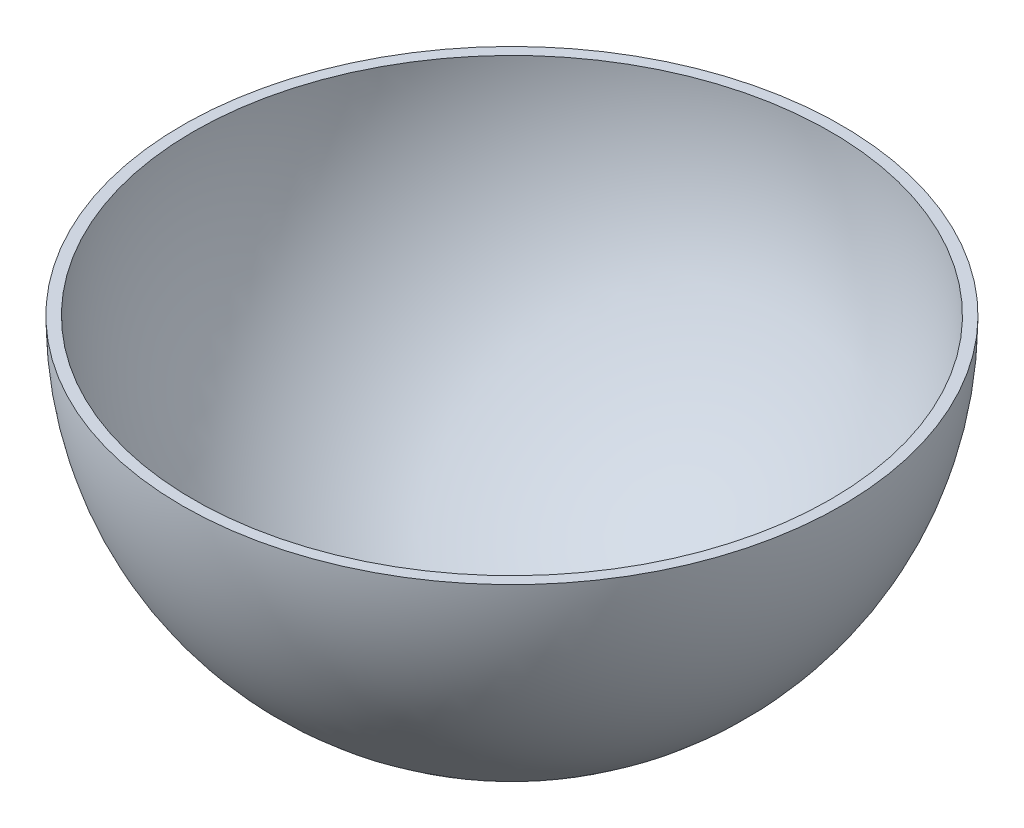
SolidWorks part; units mm, degrees
ref_plane "Front Plane" through (0, 0, 0) normal (0, 0, 1) x (1, 0, 0)
ref_plane "Top Plane" through (0, 0, 0) normal (0, 1, 0) x (1, 0, 0)
ref_plane "Right Plane" through (0, 0, 0) normal (1, 0, 0) x (0, 0, -1)
sketch "Sketch1" plane through (0, 0, 0) normal (0, 1, 0) x (1, 0, 0)
  line L0 (0, 0) -> (0, 38.1)
  line L1 (0, 0) -> (0, -38.1)
  arc A0 (0, 38.1) -> (0, -38.1) centre (0, 0) ccw
  dimension "D1" = 76.2
revolve "Revolve1" add sketch "Sketch1" angle 180 about L1
sketch "Sketch2" plane through (0, 0, 0) normal (0, 1, 0) x (1, 0, 0)
  line L0 (0, 36.83) -> (0, -36.83)
  arc A0 (0, 36.83) -> (0, -36.83) centre (0, 0) ccw
  dimension "D1" = 73.66
revolve "Cut-Revolve1" cut sketch "Sketch2" angle 180 about L0
